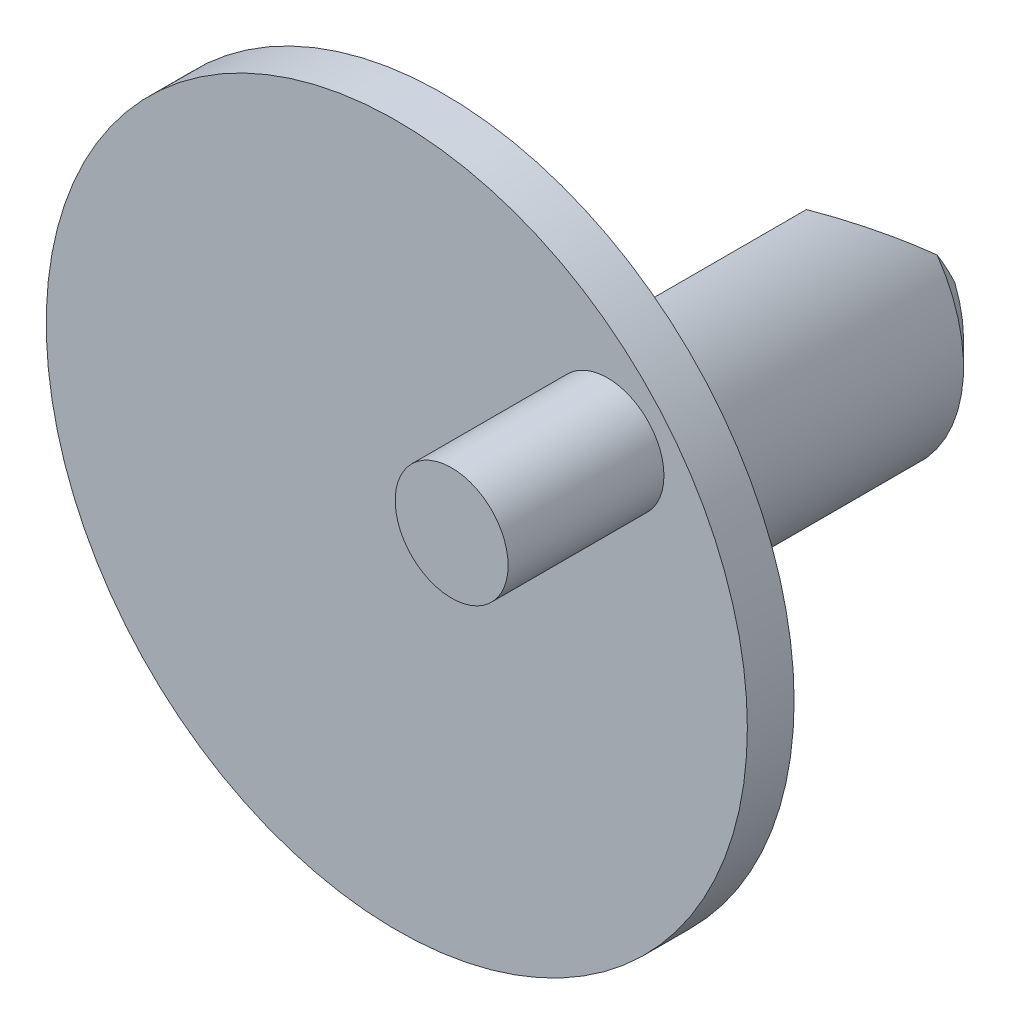
SolidWorks part; units mm, degrees
ref_plane "Front Plane" through (0, 0, 0) normal (0, 0, 1) x (1, 0, 0)
ref_plane "Top Plane" through (0, 0, 0) normal (0, 1, 0) x (1, 0, 0)
ref_plane "Right Plane" through (0, 0, 0) normal (1, 0, 0) x (0, 0, -1)
sketch "Sketch1" plane through (0, 0, 0) normal (0, 0, 1) x (1, 0, 0)
  circle A0 centre (0, 0) radius 11.43
  dimension "D1" = 22.86
extrude "Boss-Extrude1" add sketch "Sketch1" against normal blind 1.524
sketch "Sketch2" plane through (0, 0, -1.524) normal (0, 0, -1) x (-1, 0, 0)
  line L0 (-2.0525, 4.2975) -> (4.2975, -2.0525)
  line L1 (0, 0) -> (1.1225, 1.1225) construction
  line L2 (0, 0) -> (8.5579, 0) construction
  line L3 (0, 0) -> (-3.3676, -3.3676) construction
  arc A0 (-2.0525, 4.2975) -> (4.2975, -2.0525) centre (0, 0) ccw
  dimension "D1" = 9.525
  dimension "D2" = 45
  dimension "D3" = 6.35
extrude "Boss-Extrude2" add sketch "Sketch2" along normal blind 12.954
chamfer "Chamfer1" distance 3.175 angle 45 1 edges at (-1.1225, 1.1225, -14.478)
chamfer "Chamfer2" distance 0.762 angle 45 1 edges at (3.3676, -3.3676, -14.478)
sketch "Sketch3" plane through (0, 0, 0) normal (0, 0, 1) x (1, 0, 0)
  line L0 (0, 0) -> (6.8685, 5.7634) construction
  line L1 (0, 0) -> (8.1099, 0) construction
  circle A0 centre (6.8685, 5.7634) radius 1.8415
  dimension "D1" = 3.683
  dimension "D2" = 8.9662
  dimension "D3" = 40
extrude "Boss-Extrude3" add sketch "Sketch3" along normal blind 5.08
